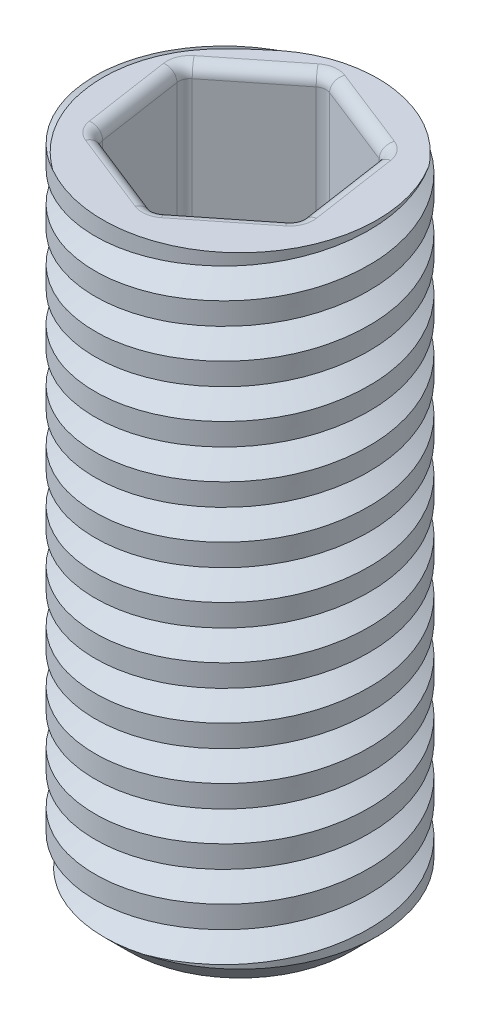
SolidWorks part; units mm, degrees
ref_plane "Plano frontal" through (0, 0, 0) normal (0, 0, 1) x (1, 0, 0)
ref_plane "Plano superior" through (0, 0, 0) normal (0, 1, 0) x (1, 0, 0)
ref_plane "Plano direito" through (0, 0, 0) normal (1, 0, 0) x (0, 0, -1)
sketch "Esboço1" plane through (0, 0, 0) normal (0, 1, 0) x (1, 0, 0)
  circle A0 centre (0, 0) radius 2.1
  dimension "D1" = 4.2
extrude "Ressalto-extrusão1" add sketch "Esboço1" along normal blind 9.9
chamfer "Chanfro1" distance 0.4 angle 45 1 edges at (0, 0, 2.1)
sketch "Esboço7" plane through (0, 0, 0) normal (0, 1, 0) x (1, 0, 0)
  circle A2 centre (0, 0) radius 2.1
  circle A3 centre (0, 0) radius 2.1
  dimension "D1" = 0
curve "Hélice/Espiral1" pitch 0.8 height 10.4 turns 13
sketch "Esboço9" plane through (0, 0, 0) normal (0, 0, 1) x (1, 0, 0)
  line L1 (2.3054, 0.3432) -> (1.7303, 0.0231)
  line L2 (1.7298, -0.0115) -> (2.2945, -0.3495)
  line L3 (2.2945, -0.3495) -> (2.3054, 0.3432)
  circle A0 centre (2.1, 0) radius 0.2 construction
  arc A1 (1.7298, -0.0115) -> (1.7303, 0.0231) centre (1.74, 0.0056) cw
  point P7 (1.7, 0.0063)
  dimension "D2" = 0.02
  dimension "D1" = 0.4
sweep "Varredura de corte1" cut profiles "Esboço9" path "Hélice/Espiral1"
sketch "Esboço10" plane through (0, 9.9, 0) normal (0, 1, 0) x (1, 0, 0)
  line L0 (1.2207, 0.9694) -> (-0.2292, 1.5419)
  line L1 (-0.2292, 1.5419) -> (-1.4499, 0.5725)
  line L2 (-1.4499, 0.5725) -> (-1.2207, -0.9694)
  line L3 (-1.2207, -0.9694) -> (0.2292, -1.5419)
  line L4 (0.2292, -1.5419) -> (1.4499, -0.5725)
  line L5 (1.4499, -0.5725) -> (1.2207, 0.9694)
  circle A0 centre (0, 0) radius 1.35 construction
  point P1 (-0.8396, 1.0572)
  dimension "D1" = 2.7
extrude "Corte-extrusão4" cut sketch "Esboço10" against normal blind 3.5
fillet "Filete3" radius 0.18 12 edges at (-1.2207, 8.15, 0.9694) (0.2292, 8.15, 1.5419) (1.4499, 8.15, 0.5725) (1.2207, 8.15, -0.9694) (-1.4499, 8.15, -0.5725) (-0.2292, 8.15, -1.5419) (0.4958, 9.9, -1.2557) (1.3353, 9.9, -0.1985) (0.8396, 9.9, 1.0572) (-0.4958, 9.9, 1.2557) (-1.3353, 9.9, 0.1985) (-0.8396, 9.9, -1.0572)
sketch "Esboço11" plane through (0, 0, 0) normal (0, -1, 0) x (1, 0, 0)
  circle A0 centre (0, 0) radius 1.24
  dimension "D1" = 2.48
extrude "Corte-extrusão5" cut sketch "Esboço11" against normal blind 0.55 draft 45
fillet "Filete4" radius 0.18 2 edges at (0, 0, -1.24) (0, 0.55, -0.69)
